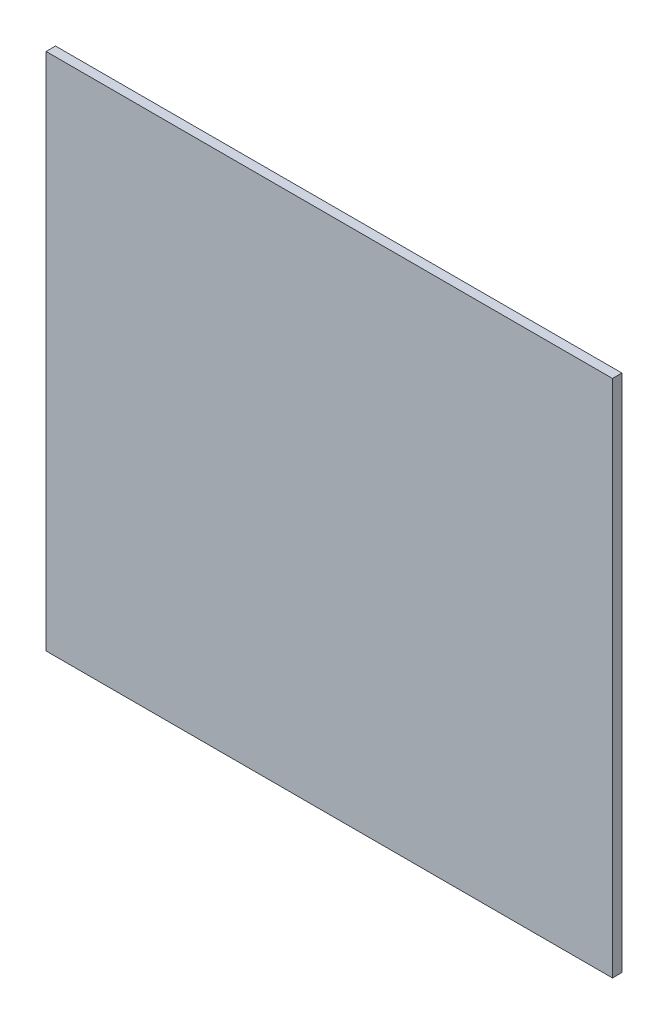
SolidWorks part; units mm, degrees
ref_plane "Plan de face" through (0, 0, 0) normal (0, 0, 1) x (1, 0, 0)
ref_plane "Plan de dessus" through (0, 0, 0) normal (0, 1, 0) x (1, 0, 0)
ref_plane "Plan de droite" through (0, 0, 0) normal (1, 0, 0) x (0, 0, -1)
sketch "Esquisse1" plane through (0, 0, 0) normal (0, 0, 1) x (1, 0, 0)
  line L1 (0, 0) -> (600, 0)
  line L2 (0, 0) -> (0, 550)
  line L3 (0, 550) -> (600, 550)
  line L4 (600, 0) -> (600, 550)
  dimension "D1" = 600
  dimension "D2" = 550
extrude "Boss.-Extru.1" add sketch "Esquisse1" along normal blind 10
